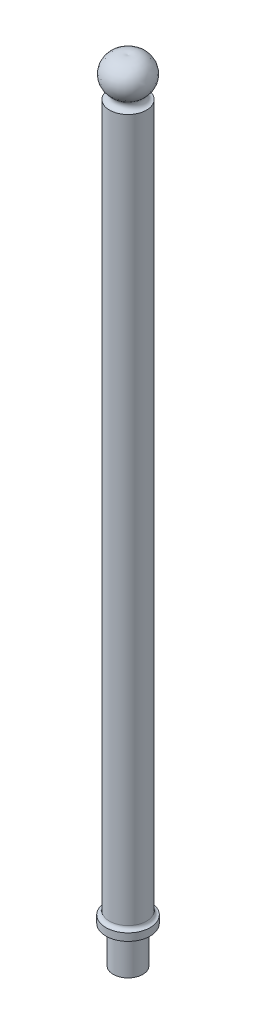
SolidWorks part; units mm, degrees
ref_plane "Front Plane" through (0, 0, 0) normal (0, 0, 1) x (1, 0, 0)
ref_plane "Top Plane" through (0, 0, 0) normal (0, 1, 0) x (1, 0, 0)
ref_plane "Right Plane" through (0, 0, 0) normal (1, 0, 0) x (0, 0, -1)
sketch "Sketch1" plane through (0, 0, 0) normal (0, 0, 1) x (1, 0, 0)
  line L0 (-6, 0) -> (0, 0)
  line L1 (0, 0) -> (0, 320.753)
  line L2 (-6, 0) -> (-6, 15)
  line L3 (-6, 15) -> (-9, 15)
  line L4 (-9, 15) -> (-9, 18)
  line L5 (-7.5, 19.5) -> (-7.5, 305)
  arc A0 (-9, 18) -> (-7.5, 19.5) centre (-9, 19.5) ccw
  arc A1 (-7.5, 305) -> (-6.2429, 308.5556) centre (-7.5, 307) ccw
  arc A2 (-6.2429, 308.5556) -> (0, 320.753) centre (-1.8431, 314) cw
  point P10 (-9, 16.5)
  point P16 (0, 319.5747)
  dimension "D6" = 1.5
  dimension "D9" = 7
  dimension "D10" = 2
  dimension "D1" = 6
  dimension "D2" = 15
  dimension "D3" = 3
  dimension "D4" = 9
  dimension "D5" = 7.5
  dimension "D7" = 290
  dimension "D8" = 9
revolve "Revolve1" add sketch "Sketch1" angle 360 about L1
cosmetic thread "Cosmetic Thread1" parameters "D2"=10.344
